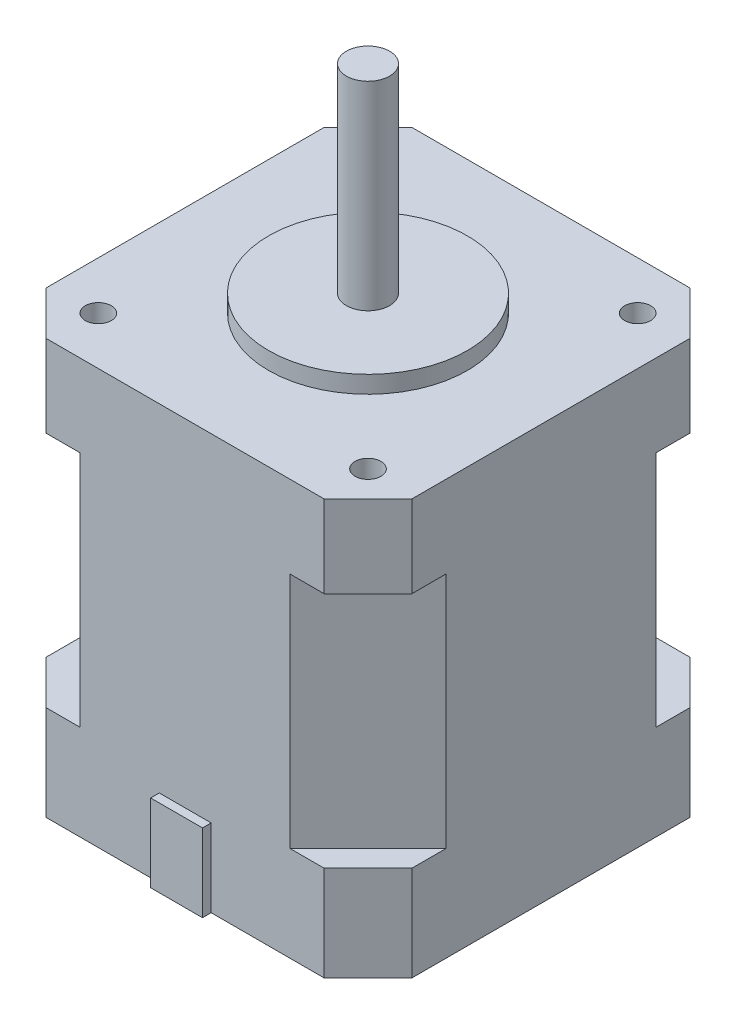
SolidWorks part; units mm, degrees
ref_plane "Front Plane" through (0, 0, 0) normal (0, 0, 1) x (1, 0, 0)
ref_plane "Top Plane" through (0, 0, 0) normal (0, 1, 0) x (1, 0, 0)
ref_plane "Right Plane" through (0, 0, 0) normal (1, 0, 0) x (0, 0, -1)
sketch "Sketch1" plane through (0, 0, 0) normal (0, 1, 0) x (1, 0, 0)
  line L1 (-21.15, 21.15) -> (21.15, 21.15)
  line L2 (-21.15, 21.15) -> (-21.15, -21.15)
  line L3 (-21.15, -21.15) -> (21.15, -21.15)
  line L4 (21.15, 21.15) -> (21.15, -21.15)
  line L5 (-21.15, 21.15) -> (21.15, -21.15) construction
  line L6 (-21.15, -21.15) -> (21.15, 21.15) construction
  point P0 (0, 0)
  dimension "D1" = 42.3
extrude "Boss-Extrude1" add sketch "Sketch1" along normal blind 48
sketch "Sketch2" plane through (0, 48, 0) normal (0, 1, 0) x (1, 0, 0)
  circle A0 centre (0, 0) radius 11.5
  dimension "D1" = 23
extrude "Boss-Extrude2" add sketch "Sketch2" along normal blind 2
sketch "Sketch3" plane through (0, 50, 0) normal (0, 1, 0) x (1, 0, 0)
  circle A0 centre (0, 0) radius 2.5
  dimension "D1" = 5
extrude "Boss-Extrude3" add sketch "Sketch3" along normal blind 23
sketch "Sketch4" plane through (0, 48, 0) normal (0, 1, 0) x (1, 0, 0)
  line L0 (21.15, 21.15) -> (-21.15, 21.15) construction
  line L1 (-21.15, 21.15) -> (-21.15, -21.15) construction
  circle A0 centre (-15.6, 15.6) radius 1.5
  dimension "D1" = 3
  dimension "D2" = 5.55
  dimension "D3" = 5.55
extrude "Cut-Extrude1" cut sketch "Sketch4" against normal blind 8
mirror "Mirror1" about plane through (0, 0, 0) normal (1, 0, 0) of "Cut-Extrude1"
mirror "Mirror3" about plane through (0, 0, 0) normal (0, 0, 1) of "Mirror1", "Cut-Extrude1"
sketch "Sketch5" plane through (0, 48, 0) normal (0, 1, 0) x (1, 0, 0)
sketch "Sketch6" plane through (0, 48, 0) normal (0, 1, 0) x (1, 0, 0)
  line L0 (-21.15, 21.15) -> (-21.15, 16.08)
  line L1 (-21.15, 21.15) -> (-21.15, -21.15) construction
  line L2 (-21.15, 21.15) -> (-16.08, 21.15)
  line L3 (21.15, 21.15) -> (-21.15, 21.15) construction
  line L4 (-16.08, 21.15) -> (-21.15, 16.08)
  dimension "D1" = 5.07
  dimension "D2" = 5.07
extrude "Cut-Extrude2" cut sketch "Sketch6" against normal blind 9.5
mirror "Mirror4" about plane through (0, 0, 0) normal (1, 0, 0) of "Cut-Extrude2"
mirror "Mirror5" about plane through (0, 0, 0) normal (0, 0, 1) of "Mirror4", "Cut-Extrude2"
sketch "Sketch7" plane through (0, 0, 0) normal (0, -1, 0) x (1, 0, 0)
  circle A0 centre (0, 0) radius 2.5
  dimension "D1" = 5
extrude "Cut-Extrude5" cut sketch "Sketch7" against normal blind 5 contours A0
sketch "Sketch8" plane through (0, 0, 0) normal (0, -1, 0) x (1, 0, 0)
  line L0 (-21.15, 21.15) -> (-21.15, 16.08)
  line L1 (-21.15, -21.15) -> (-21.15, 21.15) construction
  line L2 (-21.15, 21.15) -> (-16.08, 21.15)
  line L3 (-21.15, 21.15) -> (21.15, 21.15) construction
  line L4 (-16.08, 21.15) -> (-21.15, 16.08)
  dimension "D1" = 5.07
  dimension "D2" = 5.07
extrude "Cut-Extrude6" cut sketch "Sketch8" against normal blind 11
mirror "Mirror6" about plane through (0, 0, 0) normal (1, 0, 0) of "Cut-Extrude6"
mirror "Mirror7" about plane through (0, 0, 0) normal (0, 0, 1) of "Mirror6", "Cut-Extrude6"
sketch "Sketch10" plane through (0, 38.5, 0) normal (0, 1, 0) x (1, 0, 0)
  line L0 (-21.15, 21.15) -> (-12.15, 21.15)
  line L1 (16.08, 21.15) -> (-16.08, 21.15) construction
  line L2 (-21.15, 21.15) -> (-21.15, 12.15)
  line L3 (-21.15, 16.08) -> (-21.15, -16.08) construction
  line L4 (-21.15, 12.15) -> (-12.15, 21.15)
  dimension "D1" = 9
  dimension "D2" = 9
extrude "Cut-Extrude7" cut sketch "Sketch10" against normal up to surface (27.5 mm away) up to face at (-19.46, 11, -19.46)
sketch "Sketch11" plane through (0, 38.5, 0) normal (0, 1, 0) x (1, 0, 0)
  line L0 (21.15, 21.15) -> (12.15, 21.15)
  line L1 (21.15, 21.15) -> (21.15, 12.15)
  line L2 (21.15, -16.08) -> (21.15, 16.08) construction
  line L3 (21.15, 12.15) -> (12.15, 21.15)
  dimension "D1" = 9
  dimension "D2" = 9
extrude "Cut-Extrude8" cut sketch "Sketch11" against normal up to surface (27.5 mm away) up to face at (19.46, 11, -19.46)
sketch "Sketch12" plane through (0, 38.5, 0) normal (0, 1, 0) x (1, 0, 0)
  line L0 (-21.15, -21.15) -> (-12.15, -21.15)
  line L1 (-16.08, -21.15) -> (16.08, -21.15) construction
  line L2 (-21.15, -21.15) -> (-21.15, -12.15)
  line L3 (-21.15, 16.08) -> (-21.15, -16.08) construction
  line L4 (-21.15, -12.15) -> (-12.15, -21.15)
  dimension "D1" = 9
  dimension "D2" = 9
extrude "Cut-Extrude9" cut sketch "Sketch12" against normal up to surface (27.5 mm away) up to face at (-19.46, 11, 19.46)
sketch "Sketch13" plane through (0, 38.5, 0) normal (0, 1, 0) x (1, 0, 0)
  line L0 (21.15, -21.15) -> (21.15, -12.15)
  line L1 (21.15, -16.08) -> (21.15, 16.08) construction
  line L2 (21.15, -21.15) -> (12.15, -21.15)
  line L3 (-16.08, -21.15) -> (16.08, -21.15) construction
  line L4 (12.15, -21.15) -> (21.15, -12.15)
  dimension "D1" = 9
  dimension "D2" = 9
extrude "Cut-Extrude10" cut sketch "Sketch13" against normal up to surface (27.5 mm away) up to face at (19.46, 11, 19.46)
sketch "Sketch14" plane through (0, 0, 21.15) normal (0, 0, 1) x (1, 0, 0)
  line L0 (0, 0) -> (-3, 0)
  line L1 (-16.08, 0) -> (16.08, 0) construction
  line L2 (0, 0) -> (3, 0)
  line L3 (3, 0) -> (3, 9)
  line L4 (3, 9) -> (-3, 9)
  line L5 (-3, 9) -> (-3, 0)
  dimension "D1" = 3
  dimension "D2" = 3
  dimension "D3" = 9
  dimension "D4" = 6
extrude "Boss-Extrude4" add sketch "Sketch14" along normal blind 1
